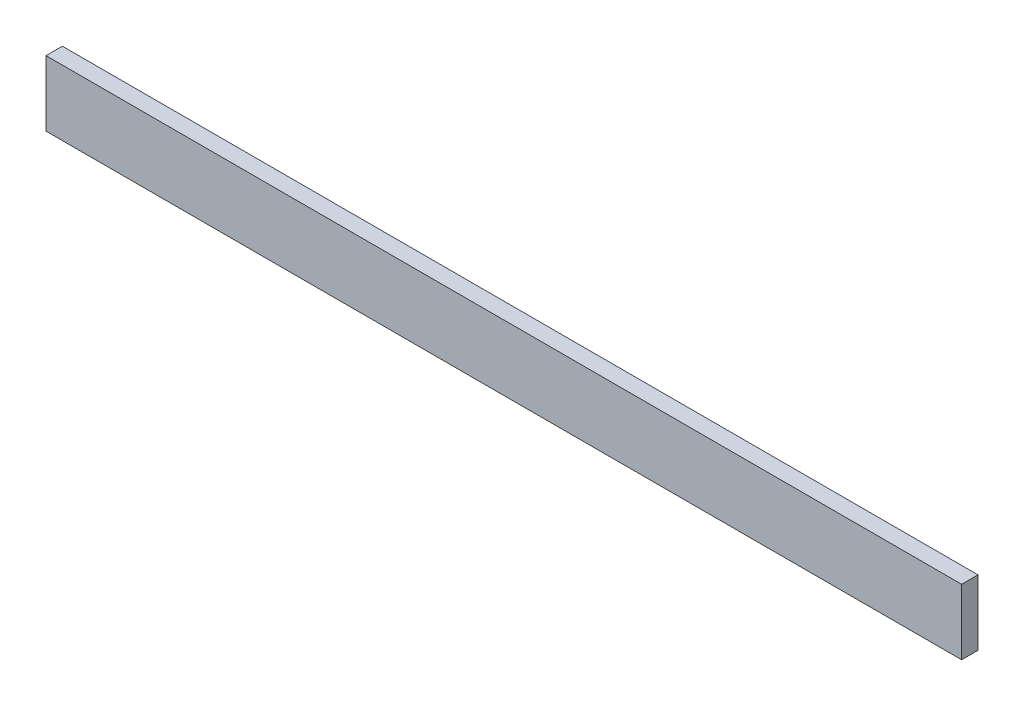
SolidWorks part; units mm, degrees
ref_plane "Front Plane" through (0, 0, 0) normal (0, 0, 1) x (1, 0, 0)
ref_plane "Top Plane" through (0, 0, 0) normal (0, 1, 0) x (1, 0, 0)
ref_plane "Right Plane" through (0, 0, 0) normal (1, 0, 0) x (0, 0, -1)
sketch "Sketch1" plane through (0, 0, 0) normal (0, 0, 1) x (1, 0, 0)
  line L1 (-88.9, -6.35) -> (88.9, -6.35)
  line L2 (-88.9, -6.35) -> (-88.9, 6.35)
  line L3 (-88.9, 6.35) -> (88.9, 6.35)
  line L4 (88.9, -6.35) -> (88.9, 6.35)
  line L5 (-88.9, -6.35) -> (88.9, 6.35) construction
  line L6 (-88.9, 6.35) -> (88.9, -6.35) construction
  point P0 (0, 0)
  dimension "D1" = 177.8
  dimension "D2" = 12.7
extrude "Boss-Extrude1" add sketch "Sketch1" along normal blind 3.175
